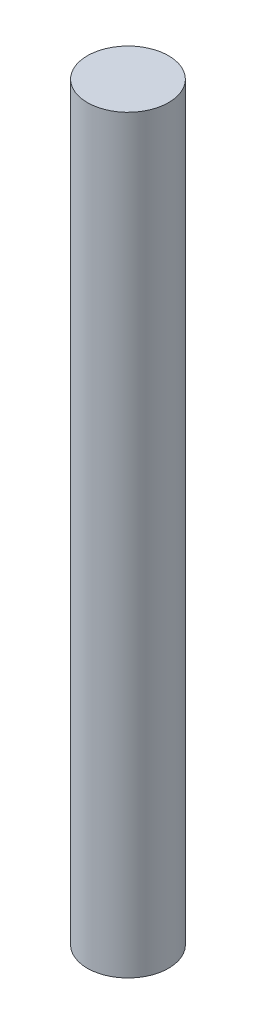
SolidWorks part; units mm, degrees
ref_plane "Front Plane" through (0, 0, 0) normal (0, 0, 1) x (1, 0, 0)
ref_plane "Top Plane" through (0, 0, 0) normal (0, 1, 0) x (1, 0, 0)
ref_plane "Right Plane" through (0, 0, 0) normal (1, 0, 0) x (0, 0, -1)
sketch "Sketch1" plane through (0, 0, 0) normal (0, 1, 0) x (1, 0, 0)
  circle A0 centre (0, 0) radius 1.95
  dimension "D1" = 3.9
extrude "Boss-Extrude1" add sketch "Sketch1" along normal blind 36
